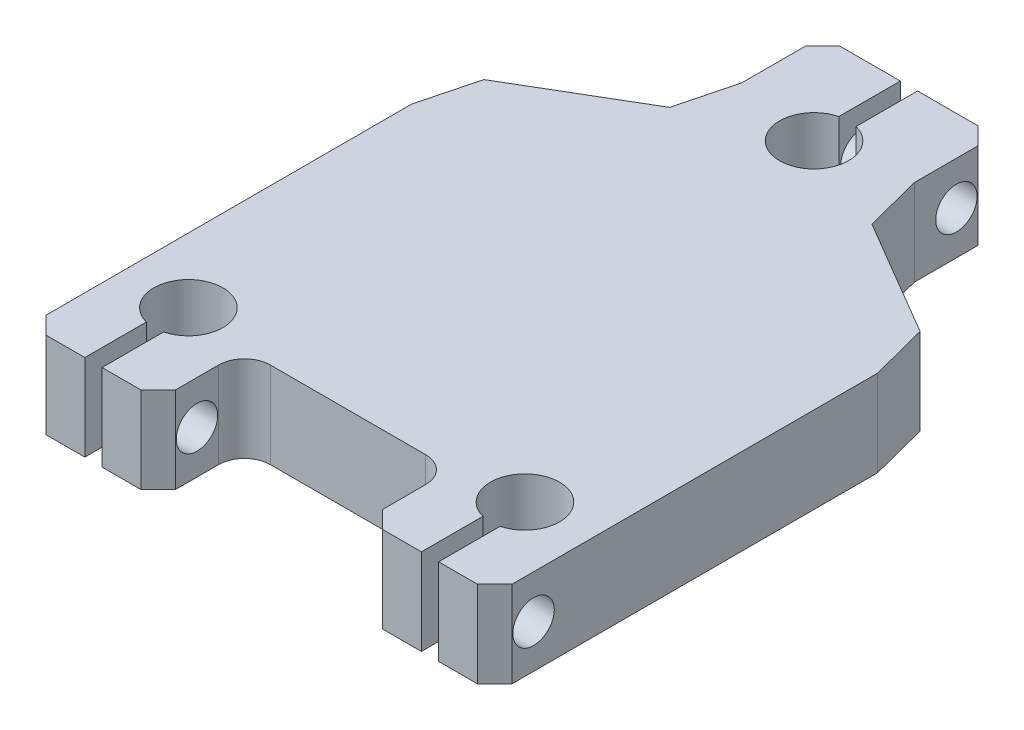
SolidWorks part; units mm, degrees
ref_plane "Front Plane" through (0, 0, 0) normal (0, 0, 1) x (1, 0, 0)
ref_plane "Top Plane" through (0, 0, 0) normal (0, 1, 0) x (1, 0, 0)
ref_plane "Right Plane" through (0, 0, 0) normal (1, 0, 0) x (0, 0, -1)
sketch "Sketch1" plane through (0, 0, 0) normal (0, 1, 0) x (1, 0, 0)
  line L1 (-12, 20) -> (12, 20)
  line L2 (-12, 20) -> (-12, -20)
  line L3 (-12, -20) -> (12, -20)
  line L4 (12, 20) -> (12, -20)
  line L5 (-12, 20) -> (12, -20) construction
  line L6 (-12, -20) -> (12, 20) construction
  point P0 (0, 0)
  dimension "D1" = 24
  dimension "D2" = 40
extrude "Boss-Extrude1" add sketch "Sketch1" along normal blind 10
sketch "Sketch2" plane through (0, 0, 0) normal (0, -1, 0) x (1, 0, 0)
  line L0 (-12, -20) -> (-12, 30)
  line L5 (12, 30) -> (12, -20)
  line L6 (12, -20) -> (-12, -20)
  line L12 (-12, 30) -> (-27, 30)
  line L13 (-27, 30) -> (-27, -20)
  line L14 (-10, -45) -> (10, -45)
  line L15 (27, -20) -> (27, 30)
  line L16 (27, 30) -> (12, 30)
  line L17 (-27, -20) -> (-10, -30)
  line L18 (-10, -30) -> (-10, -45)
  line L19 (10, -45) -> (10, -30)
  line L20 (10, -30) -> (27, -20)
  line L21 (0, 0) -> (0, -45) construction
  line L22 (-19.5, 30) -> (-19.5, 19) construction
  line L23 (19.5, 19) -> (19.5, 30) construction
  circle A0 centre (0, -34) radius 4
  circle A1 centre (-19.5, 19) radius 4
  circle A2 centre (19.5, 19) radius 4
  dimension "D3" = 15
  dimension "D9" = 50
  dimension "D10" = 20
  dimension "D11" = 11
  dimension "D12" = 8
  dimension "D6" = 15
  dimension "D7" = 8
  dimension "D13" = 8
  dimension "D14" = 11
  dimension "D15" = 11
  dimension "D1" = 15
  dimension "D2" = 50
  dimension "D4" = 25
  dimension "D5" = 50
  dimension "D8" = 50
extrude "Boss-Extrude2" add sketch "Sketch2" against normal up to surface (10 mm away) up to face at (0, 10, 0)
sketch "Sketch4" plane through (0, 10, 0) normal (0, 1, 0) x (1, 0, 0)
  line L0 (27, -30) -> (12, -30) construction
  line L1 (20.5, -37.5) -> (18.5, -37.5)
  line L2 (20.5, -37.5) -> (20.5, -22.5)
  line L3 (20.5, -22.5) -> (18.5, -22.5)
  line L4 (18.5, -37.5) -> (18.5, -22.5)
  line L5 (20.5, -37.5) -> (18.5, -22.5) construction
  line L6 (20.5, -22.5) -> (18.5, -37.5) construction
  line L7 (-12, -30) -> (-27, -30) construction
  line L8 (-20.5, -37.5) -> (-18.5, -37.5)
  line L9 (-20.5, -37.5) -> (-20.5, -22.5)
  line L10 (-20.5, -22.5) -> (-18.5, -22.5)
  line L11 (-18.5, -37.5) -> (-18.5, -22.5)
  line L12 (-20.5, -37.5) -> (-18.5, -22.5) construction
  line L13 (-20.5, -22.5) -> (-18.5, -37.5) construction
  line L14 (-10, 45) -> (10, 45) construction
  line L15 (1, 37.5) -> (-1, 37.5)
  line L16 (1, 37.5) -> (1, 52.5)
  line L17 (1, 52.5) -> (-1, 52.5)
  line L18 (-1, 37.5) -> (-1, 52.5)
  line L19 (1, 37.5) -> (-1, 52.5) construction
  line L20 (1, 52.5) -> (-1, 37.5) construction
  point P0 (19.5, -30)
  point P7 (-19.5, -30)
  point P14 (0, 45)
  dimension "D1" = 15
  dimension "D2" = 2
  dimension "D3" = 15
  dimension "D4" = 2
  dimension "D5" = 15
  dimension "D6" = 2
extrude "Cut-Extrude1" cut sketch "Sketch4" against normal blind 20
sketch "Sketch5" plane through (27, 0, 0) normal (1, 0, 0) x (0, 0, -1)
  line L0 (-30, 10) -> (-30, 0) construction
  line L1 (45, 10) -> (45, 0) construction
  line L2 (-25.5, 5) -> (-30, 5) construction
  line L3 (40.5, 5) -> (45, 5) construction
  circle A0 centre (-25.5, 5) radius 2.4
  circle A1 centre (40.5, 5) radius 2.4
  dimension "D1" = 4.8
  dimension "D2" = 4.8
  dimension "D3" = 4.5
  dimension "D4" = 4.5
extrude "Cut-Extrude2" cut sketch "Sketch5" against normal blind 56
chamfer "Chamfer2" distance 2 angle 45 6 edges at (-10, 5, -45) (10, 5, -45) (27, 5, 30) (12, 5, 30) (-27, 5, 30) (-12, 5, 30)
chamfer "Chamfer3" distance 2 angle 45 4 edges at (-27, 5, -20) (27, 5, -20) (-10, 5, -30) (10, 5, -30)
fillet "Fillet2" radius 3 2 edges at (12, 5, 20) (-12, 5, 20)
